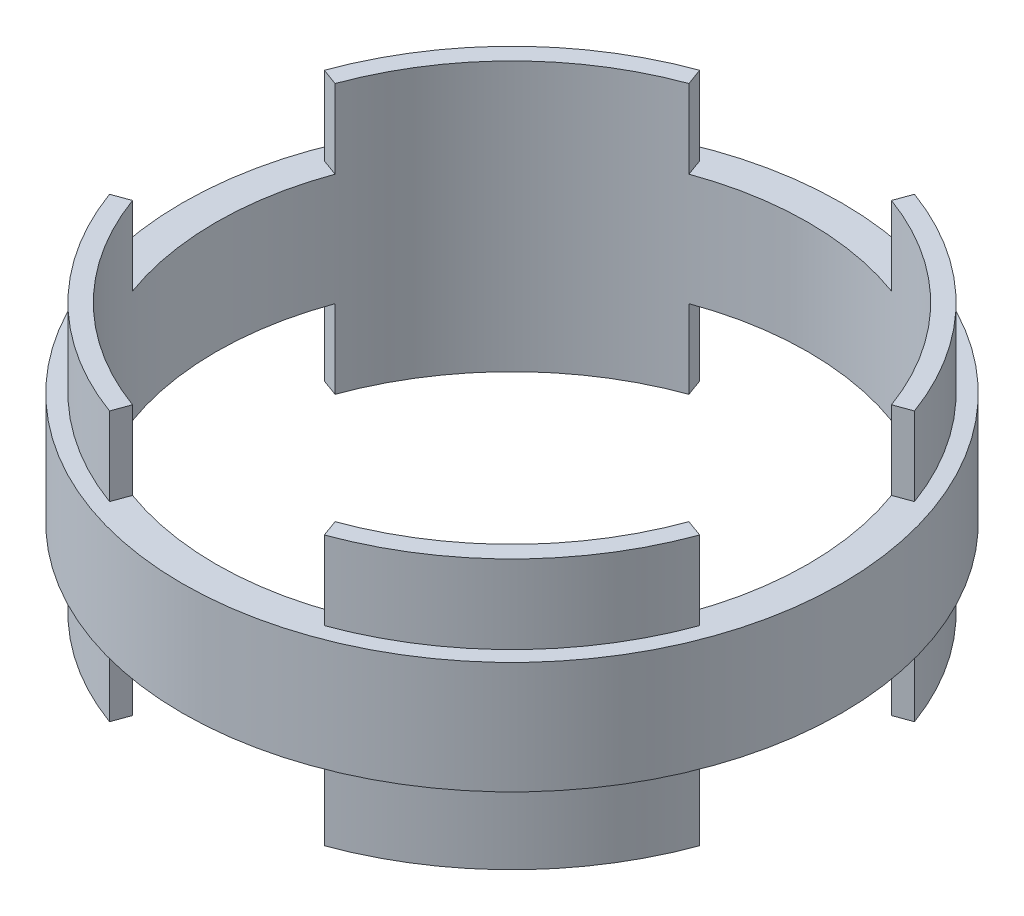
SolidWorks part; units mm, degrees
ref_plane "Front Plane" through (0, 0, 0) normal (0, 0, 1) x (1, 0, 0)
ref_plane "Top Plane" through (0, 0, 0) normal (0, 1, 0) x (1, 0, 0)
ref_plane "Right Plane" through (0, 0, 0) normal (1, 0, 0) x (0, 0, -1)
sketch "Sketch1" plane through (0, 0, 0) normal (0, 1, 0) x (1, 0, 0)
  circle A0 centre (0, 0) radius 93.345
  circle A1 centre (0, 0) radius 83.82
  dimension "D1" = 186.69
  dimension "D2" = 167.64
extrude "Boss-Extrude1" add sketch "Sketch1" along normal mid plane 31.75
sketch "Sketch2" plane through (0, 0, 0) normal (0, 1, 0) x (1, 0, 0)
  circle A0 centre (0, 0) radius 88.9
  circle A1 centre (0, 0) radius 83.82
  dimension "D1" = 177.8
  dimension "D2" = 167.64
extrude "Boss-Extrude2" add sketch "Sketch2" along normal mid plane 76.2
sketch "Sketch3" plane through (0, 0, 0) normal (0, 1, 0) x (1, 0, 0)
  line L0 (0, -116.3805) -> (0, 112.0878) construction
  line L1 (-120.9117, 0) -> (128.5432, 0) construction
  line L2 (0, 0) -> (-30.4056, 83.5387)
  line L3 (0, 0) -> (30.4056, 83.5387)
  circle A5 centre (0, 0) radius 88.9 construction
  circle A6 centre (0, 0) radius 88.9 construction
  arc A7 (-30.4056, 83.5387) -> (30.4056, 83.5387) centre (0, 0) cw
  dimension "D1" = 20
  dimension "D2" = 20
extrude "Cut-Extrude1" cut sketch "Sketch3" against normal mid plane 76.2
pattern_circular "CirPattern1" count 4 over 360 about axis through (0, 38.1, 0) along (0, -1, 0) of "Cut-Extrude1"
sketch "Sketch4" plane through (0, 0, 0) normal (0, 1, 0) x (1, 0, 0)
  circle A0 centre (0, 0) radius 88.9
  circle A1 centre (0, 0) radius 83.82
extrude "Boss-Extrude3" add sketch "Sketch4" along normal mid plane 31.75
